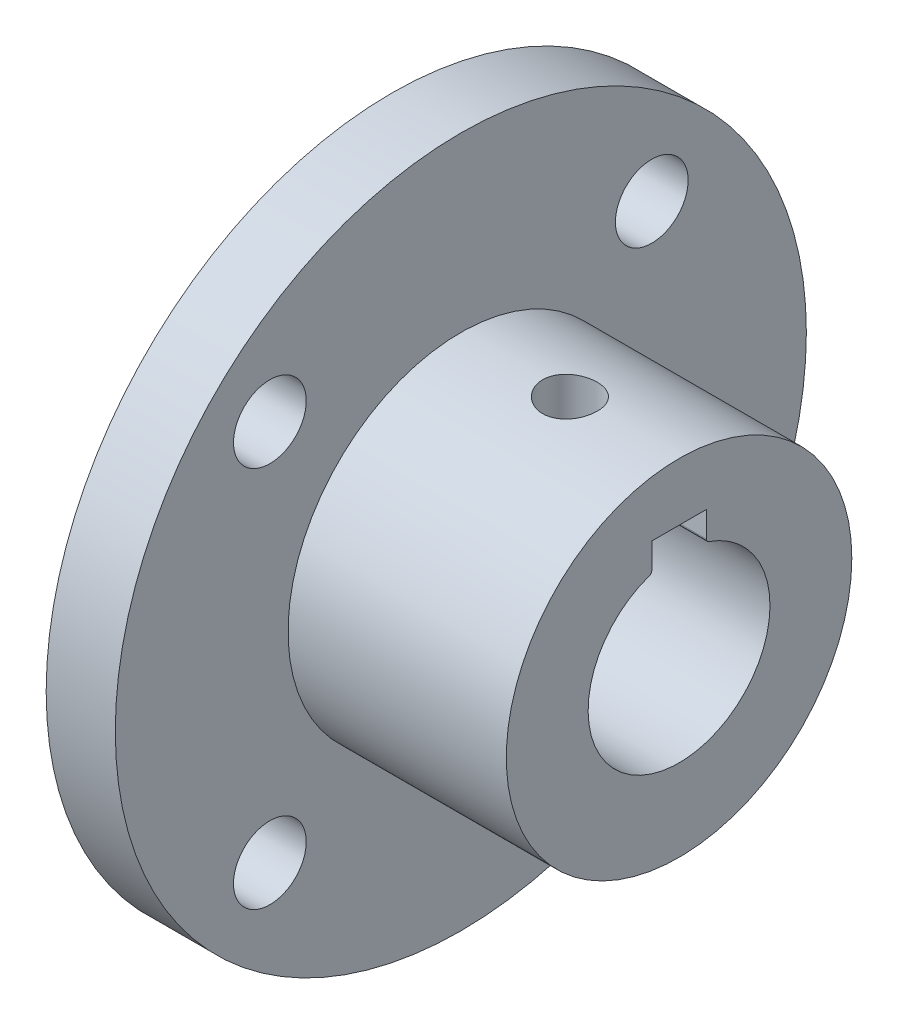
SolidWorks part; units mm, degrees
ref_plane "Piano frontale" through (0, 0, 0) normal (0, 0, 1) x (1, 0, 0)
ref_plane "Piano superiore" through (0, 0, 0) normal (0, 1, 0) x (1, 0, 0)
ref_plane "Piano destro" through (0, 0, 0) normal (1, 0, 0) x (0, 0, -1)
sketch "Sketch1" plane through (0, 0, 0) normal (1, 0, 0) x (0, 0, -1)
  circle A0 centre (0, 0) radius 9.5
  dimension "D1" = 19
extrude "Boss-Extrude1" add sketch "Sketch1" along normal blind 12
sketch "Sketch2" plane through (12, 0, 0) normal (1, 0, 0) x (0, 0, -1)
  line L0 (0, 4.7697) -> (0, 9.5) construction
  line L1 (0, 6.3197) -> (0, 4.7697) construction
  line L2 (-1.5, 6.3197) -> (1.5, 6.3197)
  line L3 (-1.5, 6.3197) -> (-1.5, 4.9143)
  line L5 (1.5, 6.3197) -> (1.5, 4.9143)
  arc A0 (-1.6346, 4.7253) -> (1.6346, 4.7253) centre (0, 0) ccw
  circle A1 centre (0, 0) radius 9.5 construction
  arc A2 (-1.6346, 4.7253) -> (-1.5, 4.9143) centre (-1.7, 4.9143) ccw
  arc A3 (1.6346, 4.7253) -> (1.5, 4.9143) centre (1.7, 4.9143) cw
  point P14 (-1.5, 4.7697)
  dimension "D1" = 10
  dimension "D4" = 0.2
  dimension "D5" = 0.2
  dimension "D2" = 3
  dimension "D3" = 1.55
sketch "Sketch4" plane through (0, 0, 0) normal (-1, 0, 0) x (0, 0, 1)
  line L0 (0, 10.5) -> (0, -10.5) construction
  line L1 (-10.5, 10.5) -> (10.5, 10.5) construction
  line L2 (-10.5, 10.5) -> (-10.5, -10.5) construction
  line L3 (-10.5, -10.5) -> (10.5, -10.5) construction
  line L4 (10.5, 10.5) -> (10.5, -10.5) construction
  line L5 (-10.5, 0) -> (10.5, 0) construction
  circle A0 centre (0, 0) radius 19
  circle A4 centre (-10.5, 10.5) radius 2
  circle A5 centre (10.5, 10.5) radius 2
  circle A6 centre (10.5, -10.5) radius 2
  circle A7 centre (-10.5, -10.5) radius 2
  point P8 (0, 0)
  dimension "D1" = 38
  dimension "D2" = 4
  dimension "D3" = 21
  dimension "D4" = 21
extrude "Boss-Extrude3" add sketch "Sketch4" along normal blind 3.8
extrude "Cut-Extrude2" cut sketch "Sketch2" against normal blind 20
sketch "Sketch5" plane through (0, 6.3197, 0) normal (0, -1, 0) x (1, 0, 0)
  line L0 (12, 1.5) -> (12, -1.5) construction
  circle A0 centre (6, 0) radius 1.5
  dimension "D1" = 3
  dimension "D2" = 6
extrude "Cut-Extrude3" cut sketch "Sketch5" against normal blind 5
